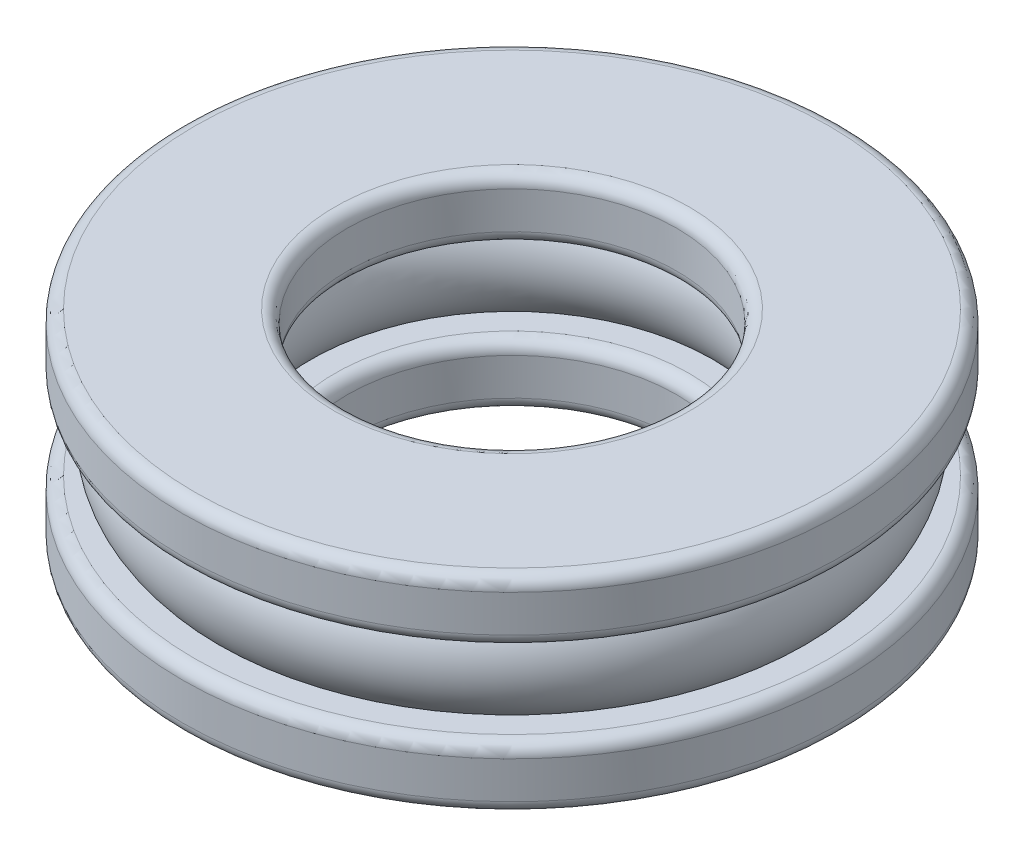
SolidWorks part; units mm, degrees
material "合金钢"
ref_plane "前视基准面" through (0, 0, 0) normal (0, 0, 1) x (1, 0, 0)
ref_plane "上视基准面" through (0, 0, 0) normal (0, 1, 0) x (1, 0, 0)
ref_plane "右视基准面" through (0, 0, 0) normal (1, 0, 0) x (0, 0, -1)
sketch "草图1" plane through (0, 0, 0) normal (0, 0, 1) x (1, 0, 0)
  line L0 (0, 6.967) -> (0, -3.6264) construction
  line L1 (4, 0) -> (8, 0)
  line L2 (8, 0) -> (8, 1.5)
  line L3 (8, 1.5) -> (7.118, 1.5)
  line L4 (4, 1.5) -> (4, 0)
  line L5 (-1.1429, 2.5) -> (10.8132, 2.5) construction
  line L6 (8, 3.5) -> (7.118, 3.5)
  line L7 (8, 5) -> (8, 3.5)
  line L8 (4, 5) -> (8, 5)
  line L9 (4, 3.5) -> (4, 5)
  line L10 (4.882, 1.5) -> (4, 1.5)
  line L11 (4.882, 3.5) -> (4, 3.5)
  arc A0 (7.118, 1.5) -> (7.118, 3.5) centre (6, 2.5) ccw
  arc A1 (4.882, 3.5) -> (4.882, 1.5) centre (6, 2.5) ccw
  point P16 (6, 0)
  dimension "D5" = 3
  dimension "D1" = 8
  dimension "D2" = 16
  dimension "D3" = 5
  dimension "D4" = 1.5
revolve "旋转1" add sketch "草图1" angle 360 about L0
fillet "圆角1" radius 0.3 8 edges at (0, 1.5, 4) (0, 3.5, 4) (0, 1.5, 8) (0, 3.5, 8) (0, 0, 4) (0, 0, 8) (0, 5, 4) (0, 5, 8)
